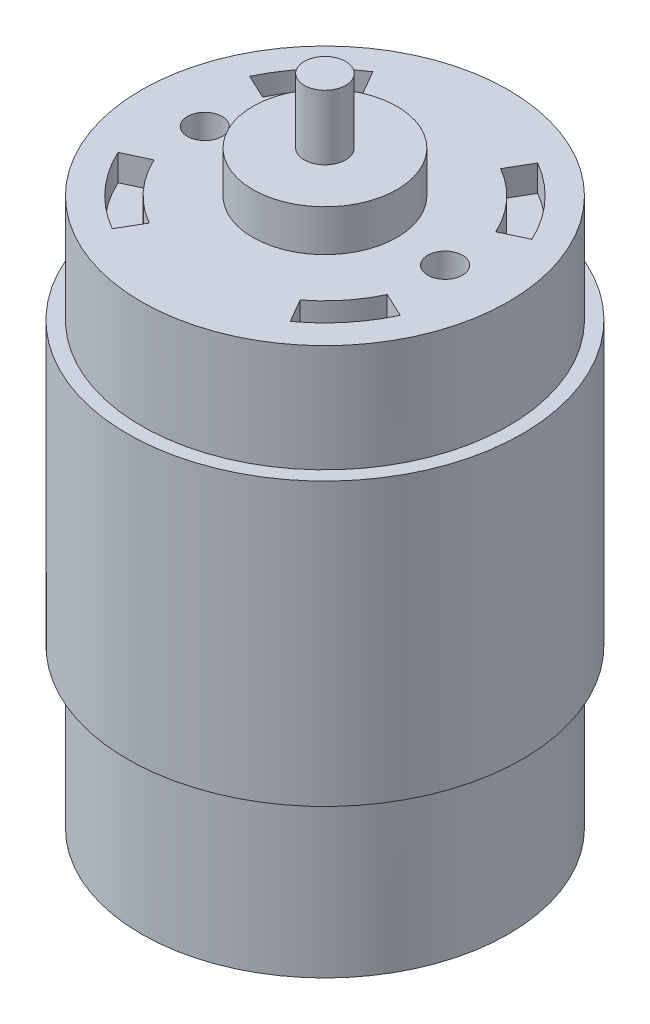
SolidWorks part; units mm, degrees
ref_plane "Front Plane" through (0, 0, 0) normal (0, 0, 1) x (1, 0, 0)
ref_plane "Top Plane" through (0, 0, 0) normal (0, 1, 0) x (1, 0, 0)
ref_plane "Right Plane" through (0, 0, 0) normal (1, 0, 0) x (0, 0, -1)
sketch "Sketch2" plane through (0, 0, 0) normal (0, 1, 0) x (1, 0, 0)
  circle A0 centre (0, 0) radius 22.1488
  dimension "D1" = 44.2976
extrude "Boss-Extrude4" add sketch "Sketch2" along normal blind 66.0908
sketch "Sketch4" plane through (0, 66.0908, 0) normal (0, 1, 0) x (1, 0, 0)
  circle A0 centre (0, 0) radius 8.6995
  dimension "D1" = 17.399
extrude "Boss-Extrude5" add sketch "Sketch4" along normal blind 5.0038 contours A0
sketch "Sketch9" plane through (0, 71.0946, 0) normal (0, 1, 0) x (1, 0, 0)
  circle A0 centre (0, 0) radius 2.5019
  dimension "D1" = 5.0038
extrude "Boss-Extrude6" add sketch "Sketch9" along normal blind 7.7978
sketch "Sketch10" plane through (0, 0, 0) normal (0, -1, 0) x (1, 0, 0)
  circle A0 centre (0, 0) radius 8.7503
  dimension "D1" = 17.5006
extrude "Boss-Extrude7" add sketch "Sketch10" along normal blind 6.7056
sketch "Sketch11" plane through (0, -6.7056, 0) normal (0, -1, 0) x (1, 0, 0)
  circle A0 centre (0, 0) radius 2.5019
  dimension "D1" = 5.0038
extrude "Boss-Extrude8" add sketch "Sketch11" along normal blind 2.413
ref_plane "Plane2" through (0, 53.1114, 0) normal (0, -1, 0) x (-1, 0, 0)
sketch "Sketch12" plane through (0, 53.1114, 0) normal (0, -1, 0) x (-1, 0, 0)
  circle A0 centre (0, 0) radius 23.8125
  dimension "D1" = 47.625
extrude "Boss-Extrude9" add sketch "Sketch12" along normal blind 34.0106
sketch "Sketch13" plane through (0, 66.0908, 0) normal (0, 1, 0) x (1, 0, 0)
  line L0 (-29.6451, 0) -> (29.6451, 0) construction
  line L1 (0, -27.354) -> (0, 29.9922) construction
  circle A0 centre (-14.5034, 0) radius 2.0955
  circle A1 centre (0, 0) radius 14.5034 construction
  circle A2 centre (14.5034, 0) radius 2.0955
  dimension "D1" = 4.191
  dimension "D2" = 29.0068
extrude "Cut-Extrude1" cut sketch "Sketch13" against normal blind 3.175
sketch "Sketch14" plane through (0, 66.0908, 0) normal (0, 1, 0) x (1, 0, 0)
  line L0 (-17.0333, -7.9428) -> (-14.07, -6.561)
  line L1 (-9.3971, -16.2762) -> (-7.7623, -13.4446)
  line L2 (-24.8296, 0) -> (26.0831, 0) construction
  line L3 (0, -32.9776) -> (0, 32.0133) construction
  line L4 (-17.0333, 7.9428) -> (-14.07, 6.561)
  line L5 (-10.0803, 15.8622) -> (-8.4437, 13.0275)
  line L6 (7.7623, 13.4446) -> (9.3971, 16.2762)
  line L7 (14.07, 6.561) -> (17.0333, 7.9428)
  line L8 (9.3859, -12.3659) -> (11.0315, -15.216)
  line L9 (14.07, -6.561) -> (17.0333, -7.9428)
  circle A0 centre (0, 0) radius 16.306 construction
  circle A1 centre (0, 0) radius 18.7942
  circle A2 centre (0, 0) radius 15.5245
  dimension "D1" = 65
  dimension "D2" = 30
  dimension "D3" = 30
  dimension "D4" = 65
  dimension "D5" = 30
  dimension "D6" = 65
  dimension "D7" = 65
  dimension "D8" = 30
extrude "Cut-Extrude2" cut sketch "Sketch14" against normal blind 3.175 contours A2 L0 A1 L1 | A2 L5 A1 L4 | A2 L7 A1 L6 | A2 L8 A1 L9
sketch "Sketch15" plane through (0, 0, 0) normal (0, -1, 0) x (1, 0, 0)
  circle A0 centre (0, 0) radius 8.7503
  circle A1 centre (0, 0) radius 20.9582
  circle A2 centre (0, 0) radius 22.1488 construction
  dimension "D1" = 1.1906
extrude "Cut-Extrude3" cut sketch "Sketch15" against normal blind 3.175
sketch "Sketch16" plane through (0, -6.7056, 0) normal (0, -1, 0) x (1, 0, 0)
  circle A0 centre (0, 0) radius 2.5019
  circle A1 centre (0, 0) radius 7.1628
  circle A2 centre (0, 0) radius 8.7503 construction
  dimension "D1" = 1.5875
extrude "Cut-Extrude4" cut sketch "Sketch16" against normal blind 2.54
sketch "Sketch18" plane through (0, 0, 0) normal (0, -1, 0) x (1, 0, 0)
  line L1 (20.5261, 3.7465) -> (17.399, 3.7465)
  line L3 (20.7021, -2.6035) -> (17.399, -2.6035)
  line L4 (17.399, 3.7465) -> (17.399, -2.6035)
  circle A0 centre (0, 0) radius 20.8652
  dimension "D1" = 17.399
  dimension "D2" = 6.35
extrude "Boss-Extrude12" add sketch "Sketch18" against normal blind 3.175 contours L3 A0 L1 L4
sketch "Sketch19" plane through (0, 0, 0) normal (0, -1, 0) x (-1, 0, 0)
  line L1 (20.7163, -3.175) -> (17.399, -3.175)
  line L3 (20.7163, 3.175) -> (17.399, 3.175)
  line L4 (17.399, -3.175) -> (17.399, 3.175)
  circle A0 centre (0, 0) radius 20.9582 construction
  arc A1 (20.7163, -3.175) -> (20.7163, 3.175) centre (0, 0) ccw
  dimension "D1" = 6.35
  dimension "D2" = 17.399
extrude "Boss-Extrude13" add sketch "Sketch19" against normal blind 3.175
sketch "Sketch20" plane through (0, 3.175, 0) normal (0, -1, 0) x (-1, 0, 0)
  circle A0 centre (-15.1765, 6.731) radius 1.5875
  dimension "D1" = 3.175
  dimension "D2" = 4.1275
  dimension "D3" = 2.2225
extrude "Cut-Extrude5" cut sketch "Sketch20" against normal blind 3.175
